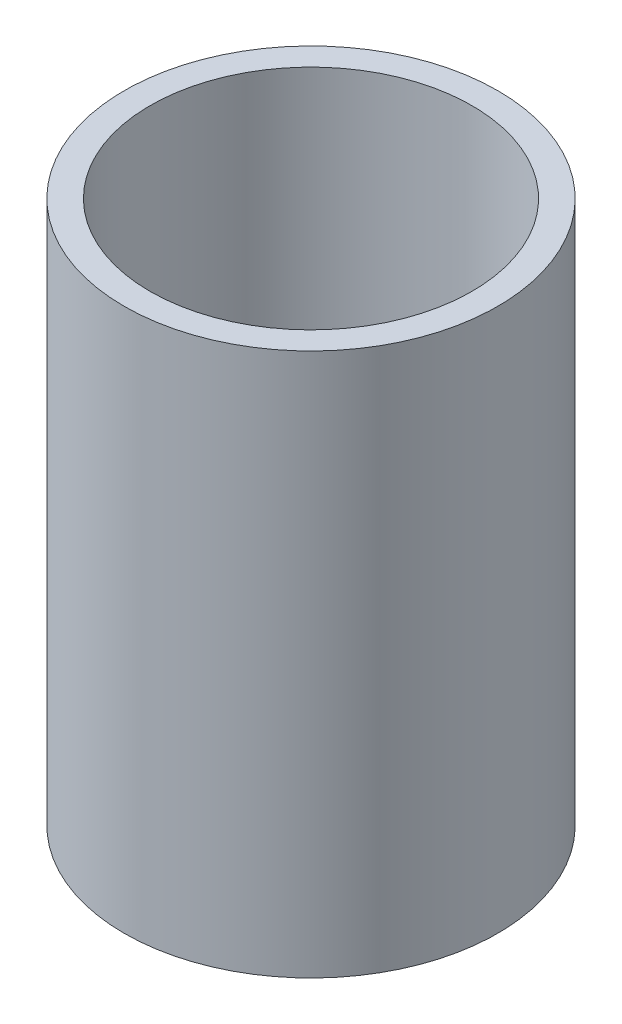
SolidWorks part; units mm, degrees
material "Corrugated Paper"
ref_plane "Front Plane" through (0, 0, 0) normal (0, 0, 1) x (1, 0, 0)
ref_plane "Top Plane" through (0, 0, 0) normal (0, 1, 0) x (1, 0, 0)
ref_plane "Right Plane" through (0, 0, 0) normal (1, 0, 0) x (0, 0, -1)
ref_axis "Axis1" through (0, 55, 0) along (0, -1, 0)
sketch "Sketch1" plane through (0, 0, 0) normal (0, 0, 1) x (1, 0, 0)
  line L1 (-45.8724, 45.6176) -> (-39.5224, 45.6176)
  line L2 (-45.8724, 45.6176) -> (-45.8724, -87.7324)
  line L3 (-45.8724, -87.7324) -> (-39.5224, -87.7324)
  line L4 (-39.5224, 45.6176) -> (-39.5224, -87.7324)
  line L5 (-38.1, 45.6176) -> (0, 45.6176) construction
  line L6 (-38.1, -87.7324) -> (0, -87.7324) construction
revolve "Revolve1" add sketch "Sketch1" angle 360 about axis through (0, 55, 0) along (0, -1, 0)
